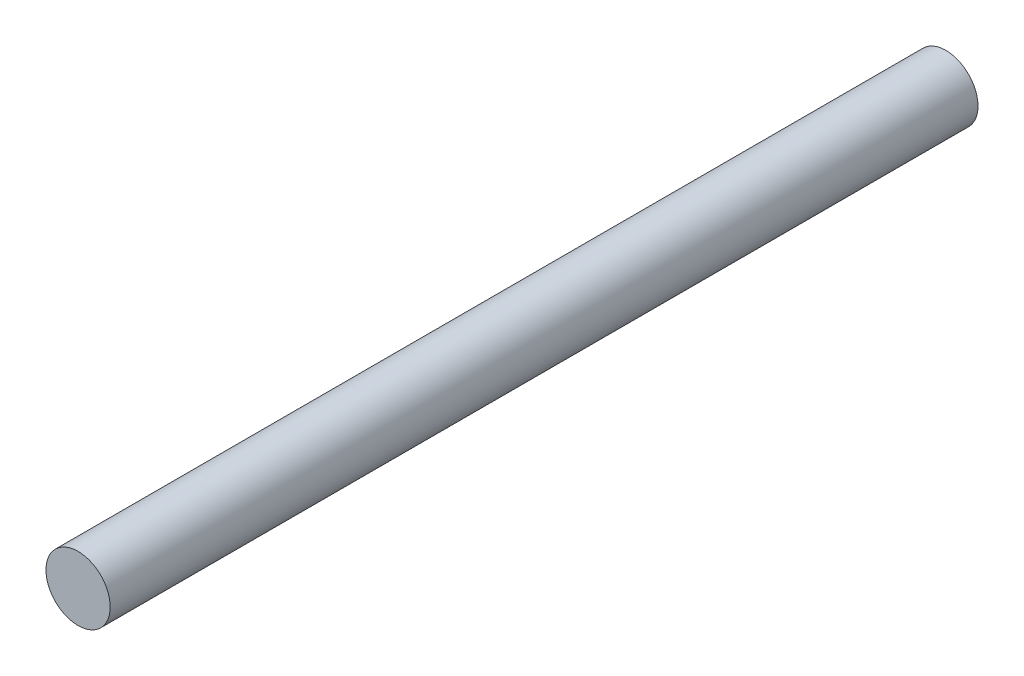
SolidWorks part; units mm, degrees
ref_plane "Plan de face" through (0, 0, 0) normal (0, 0, 1) x (1, 0, 0)
ref_plane "Plan de dessus" through (0, 0, 0) normal (0, 1, 0) x (1, 0, 0)
ref_plane "Plan de droite" through (0, 0, 0) normal (1, 0, 0) x (0, 0, -1)
sketch "Esquisse1" plane through (0, 0, 0) normal (0, 0, 1) x (1, 0, 0)
  circle A0 centre (0, 0) radius 10
  dimension "D1" = 20
extrude "Boss.-Extru.1" add sketch "Esquisse1" along normal blind 270
